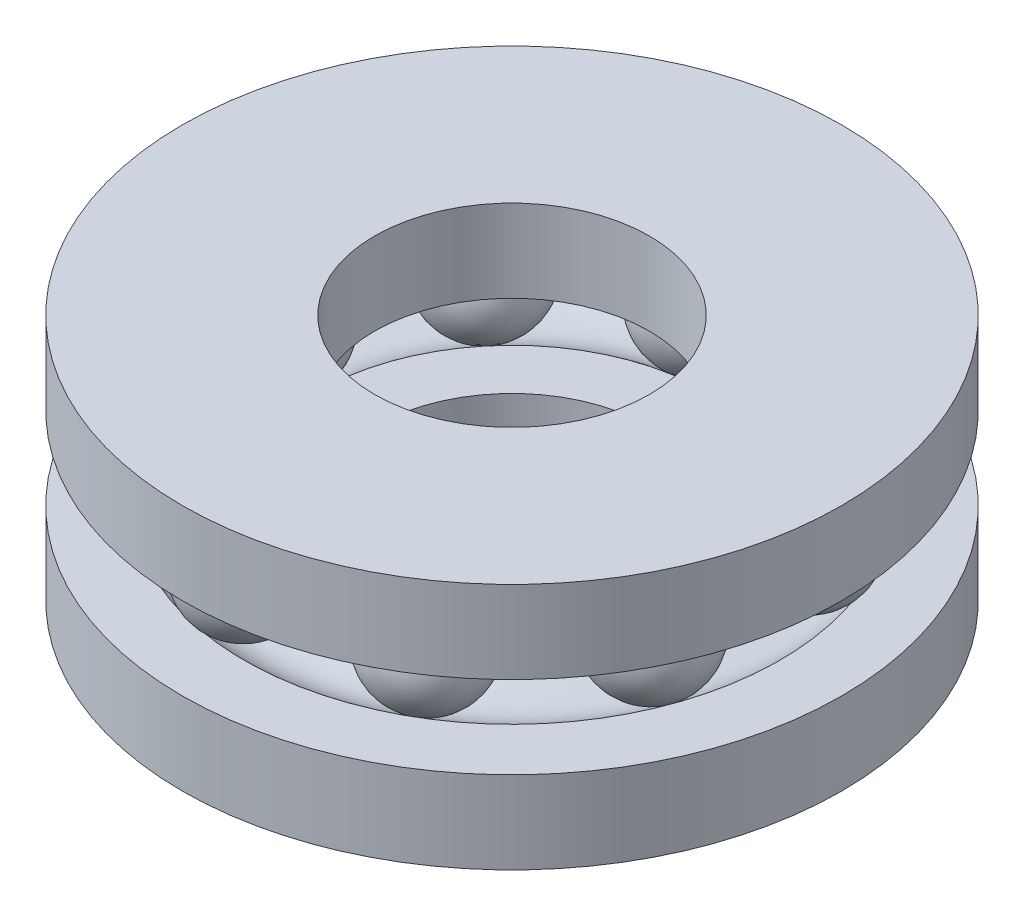
SolidWorks part; units mm, degrees
ref_plane "Alzado" through (0, 0, 0) normal (0, 0, 1) x (1, 0, 0)
ref_plane "Planta" through (0, 0, 0) normal (0, 1, 0) x (1, 0, 0)
ref_plane "Vista lateral" through (0, 0, 0) normal (1, 0, 0) x (0, 0, -1)
sketch "Croquis1" plane through (0, 0, 0) normal (0, 0, 1) x (1, 0, 0)
  line L0 (0, 0) -> (0, 30.4491) construction
  line L1 (-8.4491, 6.518) -> (-8.4491, 2.518) construction
  line L2 (-12, 6) -> (-5, 6)
  line L3 (-12, 6) -> (-12, 9)
  line L4 (-12, 9) -> (-5, 9)
  line L5 (-5, 6) -> (-5, 9)
  line L6 (-12, 3) -> (-5, 3)
  line L7 (-12, 3) -> (-12, 0)
  line L8 (-12, 0) -> (-5, 0)
  line L9 (-5, 3) -> (-5, 0)
  circle A0 centre (-8.4491, 4.518) radius 2
  point P11 (-5, 7.5)
  dimension "D4" = 4
  dimension "D1" = 24
  dimension "D2" = 10
  dimension "D3" = 9
  dimension "D5" = 3
sketch "Croquis3" plane through (0, 0, 0) normal (0, 0, 1) x (1, 0, 0)
  line L0 (-12, 3) -> (-5, 3) construction
  line L1 (-5, 3) -> (-5, 0) construction
  line L2 (-12, 0) -> (-5, 0) construction
  line L3 (-12, 3) -> (-12, 0) construction
  line L4 (-12, 6) -> (-5, 6) construction
  line L5 (-5, 6) -> (-5, 9) construction
  line L6 (-12, 9) -> (-5, 9) construction
  line L7 (-12, 6) -> (-12, 9) construction
  line L8 (-12, 3) -> (-5, 3)
  line L9 (-5, 3) -> (-5, 0)
  line L10 (-12, 0) -> (-5, 0)
  line L11 (-12, 3) -> (-12, 0)
  line L12 (-12, 6) -> (-5, 6)
  line L13 (-5, 6) -> (-5, 9)
  line L14 (-12, 9) -> (-5, 9)
  line L15 (-12, 6) -> (-12, 9)
  circle A0 centre (-8.4491, 4.518) radius 2 construction
  circle A1 centre (-8.4491, 4.518) radius 2
revolve "Revolución5" add sketch "Croquis3" angle 360 about L0
sketch "Croquis2" plane through (0, 0, 0) normal (0, 0, 1) x (1, 0, 0)
  line L1 (-8.4491, 6.518) -> (-8.4491, 2.518) construction
  line L2 (-8.4491, 6.518) -> (-8.4491, 2.518) construction
  line L3 (-8.4491, 6.518) -> (-8.4491, 2.518)
  circle A0 centre (-8.4491, 4.518) radius 2 construction
  arc A1 (-8.4491, 6.518) -> (-8.4491, 2.518) centre (-8.4491, 4.518) ccw
revolve "Revolución4" add sketch "Croquis2" angle 360 about L2
pattern_circular "MatrizC2" count 9 over 360 about axis through (0, 0, 0) along (0, 1, 0) of bodies 101
